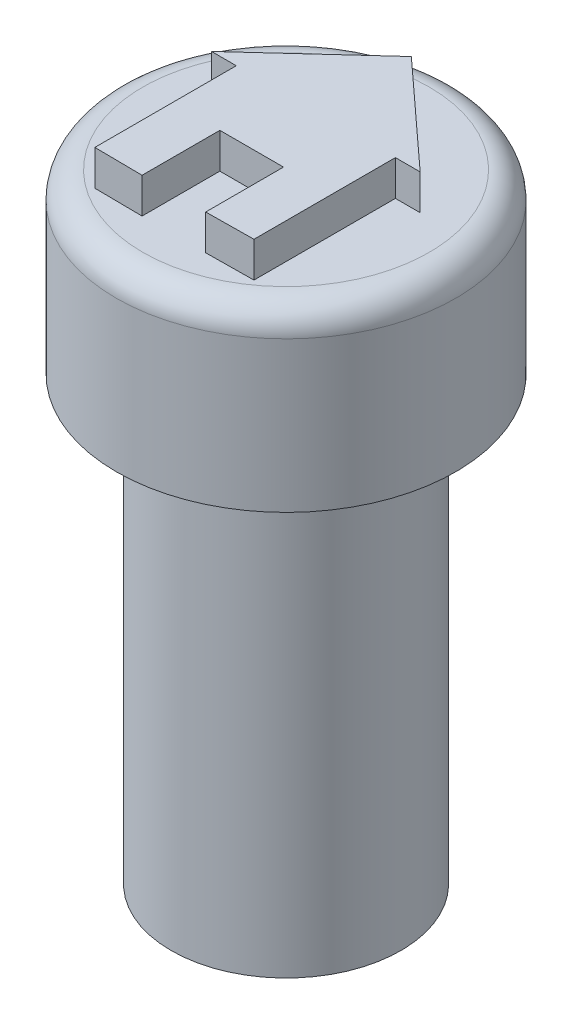
SolidWorks part; units mm, degrees
ref_plane "Front Plane" through (0, 0, 0) normal (0, 0, 1) x (1, 0, 0)
ref_plane "Top Plane" through (0, 0, 0) normal (0, 1, 0) x (1, 0, 0)
ref_plane "Right Plane" through (0, 0, 0) normal (1, 0, 0) x (0, 0, -1)
sketch "Sketch1" plane through (0, 0, 0) normal (0, 1, 0) x (1, 0, 0)
  circle A0 centre (0, 0) radius 3.25
  dimension "D1" = 6.5
extrude "Boss-Extrude1" add sketch "Sketch1" along normal blind 12.5 contours A0
sketch "Sketch2" plane through (0, 0, 0) normal (0, -1, 0) x (1, 0, 0)
  circle A1 centre (0, 0) radius 1.75
  dimension "D1" = 3.5
extrude "Cut-Extrude1" cut sketch "Sketch2" against normal blind 2.5
sketch "Sketch6" plane through (0, 12.5, 0) normal (0, 1, 0) x (1, 0, 0)
  circle A0 centre (0, 0) radius 4.8
  dimension "D1" = 9.6
extrude "Boss-Extrude2" add sketch "Sketch6" along normal blind 5 contours A0
sketch "Sketch7" plane through (0, 17.5, 0) normal (0, 1, 0) x (1, 0, 0)
  line L0 (-2.25, 0) -> (2.25, 0) construction
  line L1 (-2.25, 2.25) -> (2.25, 2.25)
  line L2 (-2.25, 2.25) -> (-2.25, -2.25)
  line L3 (-2.25, -2.25) -> (2.25, -2.25)
  line L4 (2.25, 2.25) -> (2.25, -2.25)
  line L5 (-2.25, 2.25) -> (2.25, -2.25) construction
  line L6 (-2.25, -2.25) -> (2.25, 2.25) construction
  line L7 (-2.25, 2.25) -> (-2.25, -2.25)
  line L8 (0, 0) -> (0, 2.25) construction
  dimension "D1" = 4.5
  dimension "D2" = 4.5
  dimension "D3" = 2.25
sketch "Sketch9" plane through (0, 17.5, 0) normal (0, 1, 0) x (1, 0, 0)
  line L0 (0, 0.8425) -> (0, 3.5425) construction
  line L1 (-2.25, 0.8425) -> (2.25, 0.8425)
  line L2 (-2.25, 0.8425) -> (-2.25, -3.1575)
  line L3 (-2.25, -3.1575) -> (2.25, -3.1575)
  line L4 (2.25, 0.8425) -> (2.25, -3.1575)
  line L7 (-2.95, 0.8425) -> (0, 3.5425)
  line L8 (2.25, 0.8425) -> (2.95, 0.8425)
  line L9 (-2.25, 0.8425) -> (-2.95, 0.8425)
  line L10 (0, 3.5425) -> (2.95, 0.8425)
  line L11 (0, -1.1575) -> (0.9, -1.1575) construction
  line L12 (-0.9, -3.1724) -> (0.9, -3.1724)
  line L13 (-0.9, -3.1724) -> (-0.9, -0.9724)
  line L14 (-0.9, -0.9724) -> (0.9, -0.9724)
  line L15 (0.9, -3.1724) -> (0.9, -0.9724)
  line L18 (0, -1.1575) -> (0, -0.9724) construction
  line L19 (0, -0.9724) -> (0, 0.8425) construction
  point P0 (0, -1.1575)
  point P9 (0, -2.0724)
  dimension "D1" = 4
  dimension "D2" = 4.5
  dimension "D3" = 2.7
  dimension "D4" = 0.7
  dimension "D5" = 0.7
  dimension "D6" = 2.2
  dimension "D7" = 1.8
  dimension "D8" = 0.9
  dimension "D9" = 0.1851
sketch "Sketch12" plane through (0, 17.5, 0) normal (0, 1, 0) x (1, 0, 0)
  line L0 (0, 3.5425) -> (-2.95, 0.8425)
  line L1 (-2.95, 0.8425) -> (-2.25, 0.8425)
  line L2 (-2.25, 0.8425) -> (-2.25, -3.1575)
  line L3 (-2.25, -3.1575) -> (-0.9, -3.1724)
  line L4 (-0.9, -3.1724) -> (-0.9, -0.9724)
  line L5 (-0.9, -0.9724) -> (0.9, -0.9724)
  line L6 (0.9, -0.9724) -> (0.9, -3.1724)
  line L7 (0.9, -3.1724) -> (2.25, -3.1575)
  line L8 (2.25, -3.1575) -> (2.25, 0.8425)
  line L9 (2.25, 0.8425) -> (2.95, 0.8425)
  line L10 (2.95, 0.8425) -> (0, 3.5425)
extrude "Boss-Extrude3" add sketch "Sketch12" along normal blind 1
fillet "Fillet1" radius 0.75 1 edges at (0, 17.5, 4.8)
